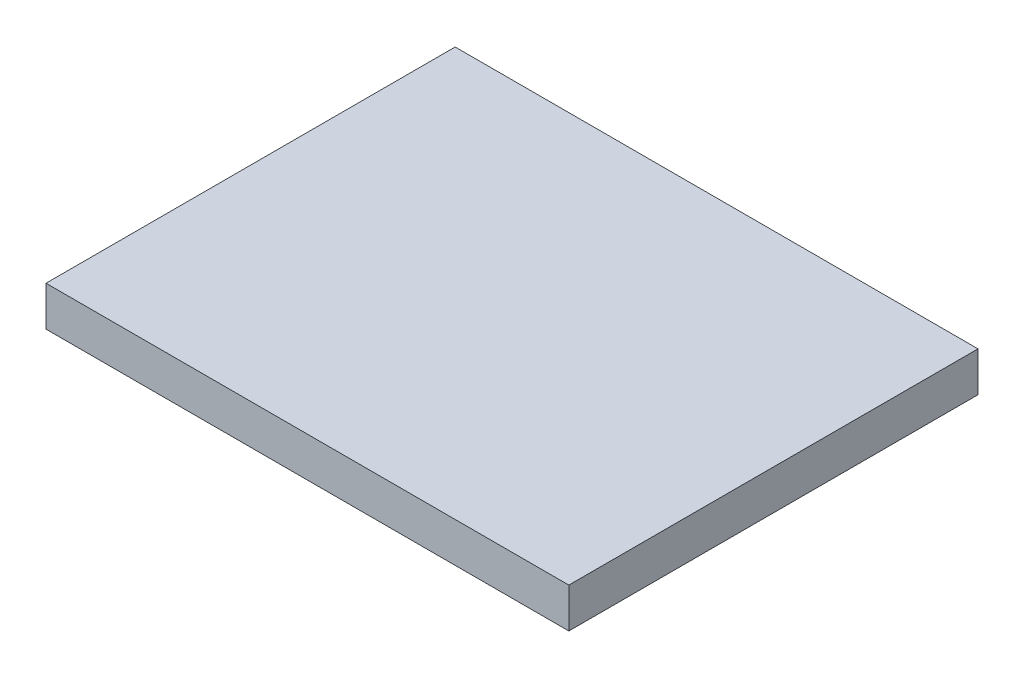
SolidWorks part; units mm, degrees
ref_plane "Plan de face" through (0, 0, 0) normal (0, 0, 1) x (1, 0, 0)
ref_plane "Plan de dessus" through (0, 0, 0) normal (0, 1, 0) x (1, 0, 0)
ref_plane "Plan de droite" through (0, 0, 0) normal (1, 0, 0) x (0, 0, -1)
sketch "Esquisse1" plane through (0, 0, 0) normal (0, 1, 0) x (1, 0, 0)
  line L1 (-23, 18) -> (23, 18)
  line L2 (-23, 18) -> (-23, -18)
  line L3 (-23, -18) -> (23, -18)
  line L4 (23, 18) -> (23, -18)
  point P4 (23, 0)
  point P6 (0, 18)
  dimension "D1" = 46
  dimension "D2" = 36
extrude "Boss.-Extru.1" add sketch "Esquisse1" along normal blind 3.5
